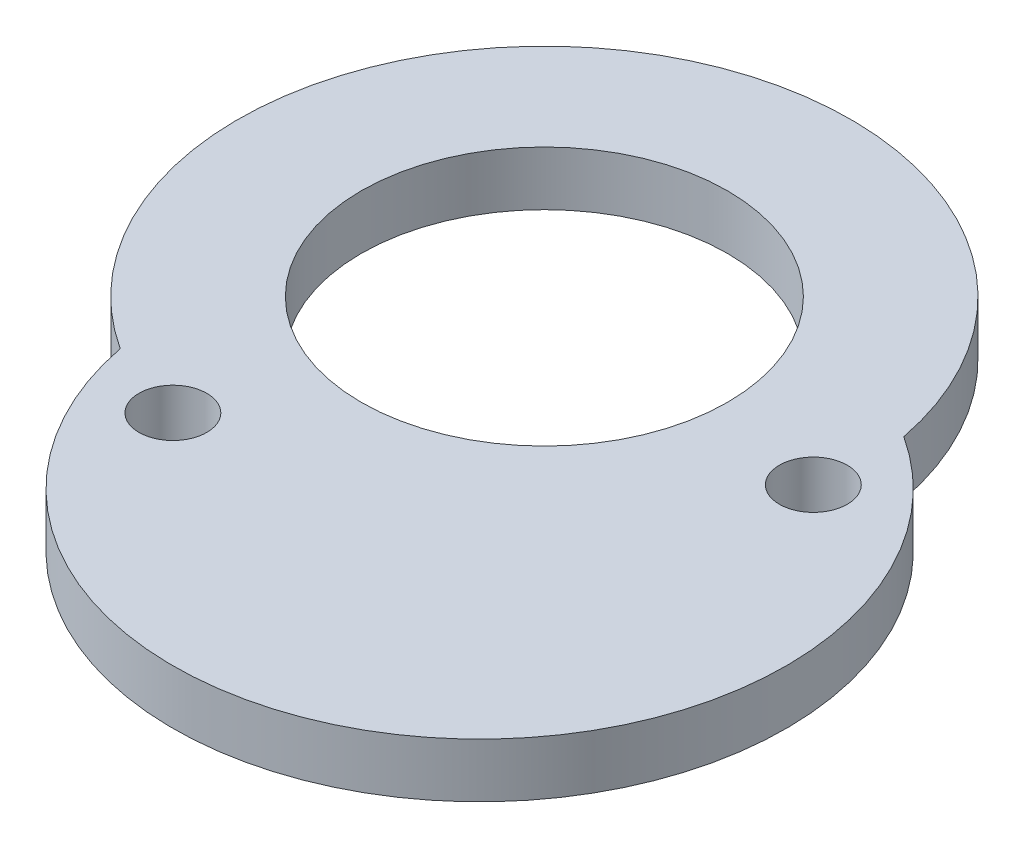
SolidWorks part; units mm, degrees
ref_plane "前视基准面" through (0, 0, 0) normal (0, 0, 1) x (1, 0, 0)
ref_plane "上视基准面" through (0, 0, 0) normal (0, 1, 0) x (1, 0, 0)
ref_plane "右视基准面" through (0, 0, 0) normal (1, 0, 0) x (0, 0, -1)
sketch "草图1" plane through (0, 0, 0) normal (0, 1, 0) x (1, 0, 0)
  arc A0 (11.0932, 2.1519) -> (-6.1508, -9.4794) centre (0, 0) ccw
  arc A1 (-6.1508, -9.4794) -> (11.0932, 2.1519) centre (4.9425, -7.3275) ccw
  circle A2 centre (0, 0) radius 6.75
  circle A3 centre (-3.1325, -10.5564) radius 1.25
  circle A4 centre (10.9612, -1.0501) radius 1.25
  dimension "D1" = 13.5
extrude "凸台-拉伸1" add sketch "草图1" along normal blind 2
